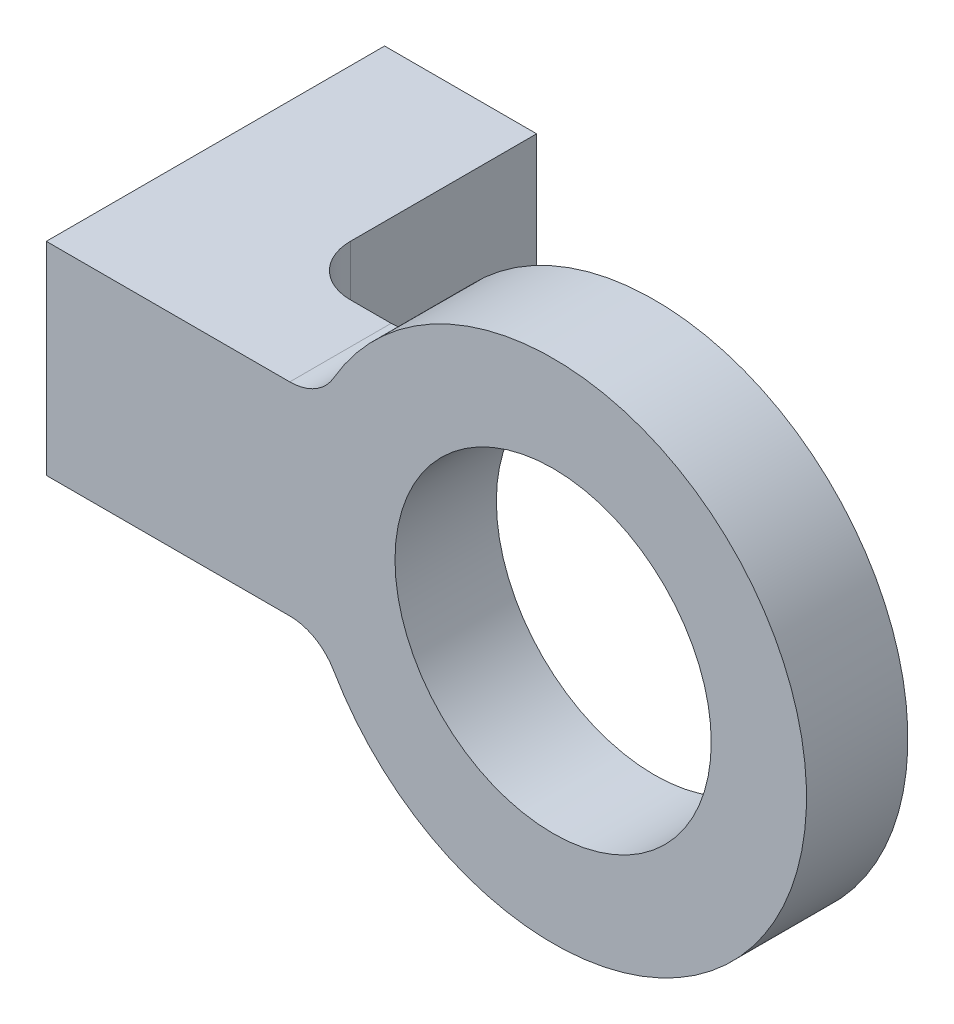
SolidWorks part; units mm, degrees
ref_plane "Front Plane" through (0, 0, 0) normal (0, 0, 1) x (1, 0, 0)
ref_plane "Top Plane" through (0, 0, 0) normal (0, 1, 0) x (1, 0, 0)
ref_plane "Right Plane" through (0, 0, 0) normal (1, 0, 0) x (0, 0, -1)
sketch "Sketch1" plane through (0, 0, 0) normal (0, 0, 1) x (1, 0, 0)
  line L0 (7.6753, 12.7) -> (0, 12.7)
  line L1 (0, 0) -> (7.6753, 0)
  line L2 (0, 0) -> (0, 12.7)
  circle A0 centre (22.225, 6.35) radius 9.906
  arc A1 (7.6753, 0) -> (7.6753, 12.7) centre (22.225, 6.35) ccw
  dimension "D3" = 19.812
  dimension "D1" = 31.75
  dimension "D2" = 22.225
  dimension "D4" = 12.7
extrude "Boss-Extrude1" add sketch "Sketch1" along normal blind 6.35
sketch "Sketch2" plane through (0, 0, 6.35) normal (0, 0, 1) x (1, 0, 0)
  line L1 (0, 12.7) -> (-9.525, 12.7)
  line L2 (0, 12.7) -> (0, 0)
  line L3 (0, 0) -> (-9.525, 0)
  line L4 (-9.525, 12.7) -> (-9.525, 0)
  line L5 (0, 0) -> (7.6753, 0) construction
  line L6 (7.6753, 12.7) -> (0, 12.7) construction
  dimension "D1" = 9.525
extrude "Boss-Extrude2" add sketch "Sketch2" against normal up to surface (21.193 mm away)
hole_wizard "#8-32 Tapped Hole1" positions "Sketch4" profile "Sketch5" tap size "#8-32" standard "ANSI Inch"
sketch "Sketch4" plane through (0, 0, -14.843) normal (0, 0, -1) x (-1, 0, 0)
  line L1 (0, 6.35) -> (9.525, 6.35) construction
  line L2 (0, 0) -> (0, 12.7) construction
  line L3 (9.525, 12.7) -> (9.525, 0) construction
  point P0 (4.7625, 6.35)
sketch "Sketch5" plane through (-4.7625, 6.35, -14.843) normal (1, 0, 0) x (0, 1, 0)
  line L0 (0, 0) -> (0, 17.8932)
  line L1 (0, 17.8932) -> (1.7272, 16.8554)
  line L2 (1.7272, 16.8554) -> (1.7272, 0)
  line L5 (1.7272, 0) -> (0, 0)
  line L10 (0, 17.8932) -> (-1.7272, 16.8554) construction
  line L11 (0, -6.35) -> (0, 107.95) construction
  dimension "Tap Drill Dia." = 3.4544
  dimension "Tap Drill Depth" = 16.8554
  dimension "Drill Angle" = 118
fillet "Fillet1" radius 3.175 3 edges at (7.6753, 12.7, 3.175) (7.6753, 0, 3.175)
